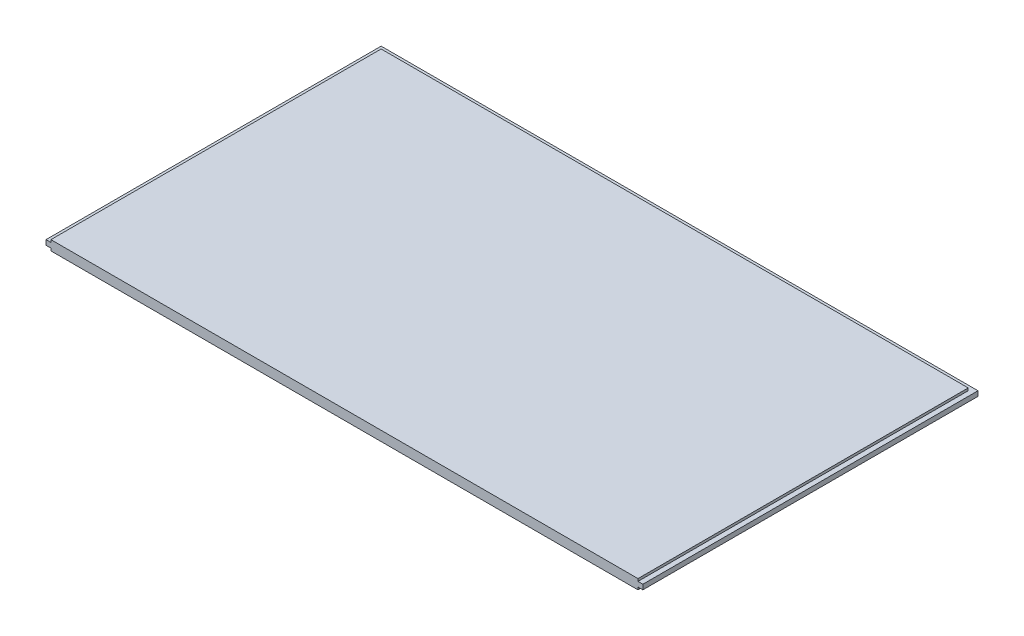
SolidWorks part; units mm, degrees
ref_plane "Front Plane" through (0, 0, 0) normal (0, 0, 1) x (1, 0, 0)
ref_plane "Top Plane" through (0, 0, 0) normal (0, 1, 0) x (1, 0, 0)
ref_plane "Right Plane" through (0, 0, 0) normal (1, 0, 0) x (0, 0, -1)
sketch "Sketch1" plane through (0, 0, 0) normal (0, 1, 0) x (1, 0, 0)
  line L1 (-344.0583, 165.6792) -> (430.6417, 165.6792)
  line L2 (-344.0583, 165.6792) -> (-344.0583, -269.2958)
  line L3 (-344.0583, -269.2958) -> (430.6417, -269.2958)
  line L4 (430.6417, 165.6792) -> (430.6417, -269.2958)
  dimension "D1" = 774.7
  dimension "D2" = 434.975
extrude "Boss-Extrude1" add sketch "Sketch1" along normal blind 12.7
sketch "Sketch2" plane through (-344.0583, 0, 0) normal (-1, 0, 0) x (0, 0, 1)
  line L1 (-165.6792, 12.7) -> (-159.3292, 12.7)
  line L2 (-165.6792, 12.7) -> (-165.6792, 9.525)
  line L3 (-165.6792, 9.525) -> (-159.3292, 9.525)
  line L4 (-159.3292, 12.7) -> (-159.3292, 9.525)
  line L5 (-165.6792, 0) -> (-159.3292, 0)
  line L6 (-165.6792, 0) -> (-165.6792, 3.175)
  line L7 (-165.6792, 3.175) -> (-159.3292, 3.175)
  line L8 (-159.3292, 0) -> (-159.3292, 3.175)
  dimension "D1" = 3.175
  dimension "D2" = 6.35
  dimension "D3" = 6.35
  dimension "D4" = 3.175
extrude "Cut-Extrude1" cut sketch "Sketch2" against normal through all
sketch "Sketch3" plane through (0, 0, 269.2958) normal (0, 0, 1) x (1, 0, 0)
  line L0 (-344.0583, 6.35) -> (49655.9417, 6.35) construction
  line L1 (-344.0583, 12.7) -> (-337.7083, 12.7)
  line L2 (-344.0583, 12.7) -> (-344.0583, 9.525)
  line L3 (-344.0583, 9.525) -> (-337.7083, 9.525)
  line L4 (-337.7083, 12.7) -> (-337.7083, 9.525)
  line L5 (-344.0583, 12.7) -> (-344.0583, 0) construction
  line L6 (43.2917, -1000) -> (43.2917, 49000) construction
  line L7 (-344.0583, 0) -> (430.6417, 0) construction
  line L8 (-337.7083, 0) -> (-337.7083, 3.175)
  line L9 (-344.0583, 3.175) -> (-337.7083, 3.175)
  line L10 (-344.0583, 0) -> (-344.0583, 3.175)
  line L11 (-344.0583, 0) -> (-337.7083, 0)
  line L12 (430.6417, 0) -> (424.2917, 0)
  line L13 (430.6417, 0) -> (430.6417, 3.175)
  line L14 (430.6417, 3.175) -> (424.2917, 3.175)
  line L15 (424.2917, 0) -> (424.2917, 3.175)
  line L16 (424.2917, 12.7) -> (424.2917, 9.525)
  line L17 (430.6417, 9.525) -> (424.2917, 9.525)
  line L18 (430.6417, 12.7) -> (430.6417, 9.525)
  line L19 (430.6417, 12.7) -> (424.2917, 12.7)
  point P10 (-344.0583, 6.35)
  point P15 (43.2917, 0)
  dimension "D1" = 3.175
  dimension "D2" = 6.35
extrude "Cut-Extrude2" cut sketch "Sketch3" against normal through all
